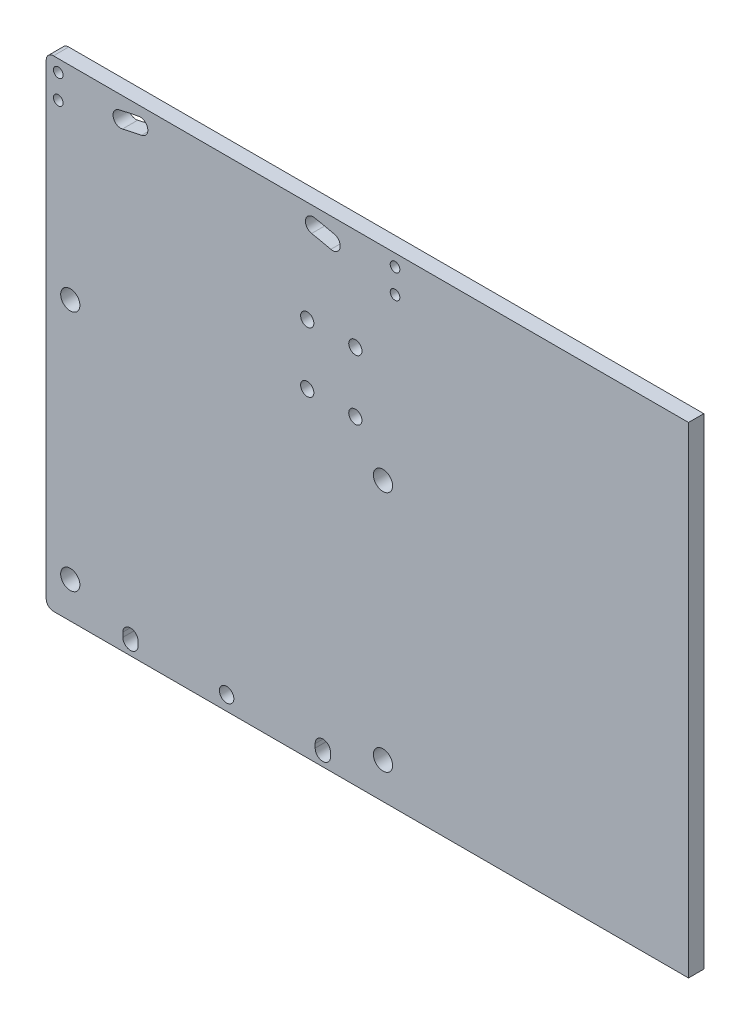
SolidWorks part; units mm, degrees
material "Plain Carbon Steel"
ref_plane "Front Plane" through (0, 0, 0) normal (0, 0, 1) x (1, 0, 0)
ref_plane "Top Plane" through (0, 0, 0) normal (0, 1, 0) x (1, 0, 0)
ref_plane "Right Plane" through (0, 0, 0) normal (1, 0, 0) x (0, 0, -1)
sketch "Sketch1" plane through (0, 0, 0) normal (0, 0, 1) x (1, 0, 0)
  line L0 (0, 0) -> (0, -65.325) construction
  line L1 (72, 134.675) -> (-72, 134.675)
  line L2 (75, 131.675) -> (75, -62.325)
  line L3 (72, -65.325) -> (-72, -65.325)
  line L4 (-75, 131.675) -> (-75, -62.325)
  line L5 (75, 134.675) -> (-75, -65.325) construction
  line L6 (75, -65.325) -> (-75, 134.675) construction
  line L7 (65, -50.325) -> (-65, -50.325) construction
  line L8 (65, -50.325) -> (65, 50.325) construction
  line L9 (65, 50.325) -> (-65, 50.325) construction
  line L10 (-65, -50.325) -> (-65, 50.325) construction
  line L11 (65, -50.325) -> (-65, 50.325) construction
  line L12 (65, 50.325) -> (-65, -50.325) construction
  line L13 (0, 34.675) -> (0, 0) construction
  circle A0 centre (-65, 50.325) radius 4
  circle A1 centre (-65, -50.325) radius 4
  circle A2 centre (65, -50.325) radius 4
  circle A3 centre (65, 50.325) radius 4
  arc A4 (-72, -65.325) -> (-75, -62.325) centre (-72, -62.325) cw
  arc A5 (75, -62.325) -> (72, -65.325) centre (72, -62.325) cw
  arc A6 (75, 131.675) -> (72, 134.675) centre (72, 131.675) ccw
  arc A7 (-72, 134.675) -> (-75, 131.675) centre (-72, 131.675) ccw
  circle A8 centre (-65, 50.325) radius 12.325 construction
  circle A9 centre (-65, -50.325) radius 12.325 construction
  point P0 (0, 0)
  point P6 (0, 0)
  point P32 (-65, -38)
  point P35 (-65, 38)
  dimension "D5" = 8
  dimension "D6" = 8
  dimension "D7" = 3
  dimension "D8" = 24.65
  dimension "D9" = 200
  dimension "D1" = 15
  dimension "D2" = 150
  dimension "D3" = 76
  dimension "D4" = 10
extrude "Boss-Extrude1" add sketch "Sketch1" along normal blind 6.35
sketch "Sketch2" plane through (0, 0, 6.35) normal (0, 0, 1) x (1, 0, 0)
  line L0 (-40, -59.325) -> (40, -59.325) construction
  line L1 (0, -59.325) -> (0, 126.675) construction
  line L2 (-40, 126.675) -> (40, 126.675) construction
  line L3 (-44.048, 125.7581) -> (0, -59.325) construction
  line L4 (0, -59.325) -> (-35.9329, 127.5033) construction
  line L5 (-39.9905, -58.4524) -> (0, -59.325) construction
  line L6 (-39.9905, -60.1976) -> (0, -59.325) construction
  line L7 (72, 134.675) -> (-72, 134.675) construction
  line L8 (-72, -65.325) -> (72, -65.325) construction
  line L9 (39.9905, -60.1976) -> (0, -59.325) construction
  line L10 (39.9905, -58.4524) -> (0, -59.325) construction
  line L11 (0, -59.325) -> (35.9329, 127.5033) construction
  line L12 (44.048, 125.7581) -> (0, -59.325) construction
  arc A4 (-35.9329, 127.5033) -> (-44.048, 125.7581) centre (0, -59.325) ccw construction
  arc A5 (-36.5335, 130.6261) -> (-44.7843, 128.8517) centre (0, -59.325) ccw
  arc A6 (-35.3323, 124.3806) -> (-43.3118, 122.6645) centre (0, -59.325) ccw
  arc A7 (-35.3323, 124.3806) -> (-36.5335, 130.6261) centre (-35.9329, 127.5033) ccw
  arc A8 (-44.7843, 128.8517) -> (-43.3118, 122.6645) centre (-44.048, 125.7581) ccw
  arc A9 (-39.9905, -58.4524) -> (-39.9905, -60.1976) centre (0, -59.325) ccw construction
  arc A10 (-43.1647, -58.3831) -> (-43.1647, -60.2669) centre (0, -59.325) ccw
  arc A11 (-36.8162, -58.5217) -> (-36.8162, -60.1283) centre (0, -59.325) ccw
  arc A12 (-36.8162, -58.5217) -> (-43.1647, -58.3831) centre (-39.9905, -58.4524) ccw
  arc A13 (-43.1647, -60.2669) -> (-36.8162, -60.1283) centre (-39.9905, -60.1976) ccw
  arc A14 (35.9329, 127.5033) -> (44.048, 125.7581) centre (0, -59.325) cw construction
  arc A15 (36.5335, 130.6261) -> (44.7843, 128.8517) centre (0, -59.325) cw
  arc A16 (35.3323, 124.3806) -> (43.3118, 122.6645) centre (0, -59.325) cw
  arc A17 (35.3323, 124.3806) -> (36.5335, 130.6261) centre (35.9329, 127.5033) cw
  arc A18 (44.7843, 128.8517) -> (43.3118, 122.6645) centre (44.048, 125.7581) cw
  arc A19 (39.9905, -58.4524) -> (39.9905, -60.1976) centre (0, -59.325) cw construction
  arc A20 (43.1647, -58.3831) -> (43.1647, -60.2669) centre (0, -59.325) cw
  arc A21 (36.8162, -58.5217) -> (36.8162, -60.1283) centre (0, -59.325) cw
  arc A22 (36.8162, -58.5217) -> (43.1647, -58.3831) centre (39.9905, -58.4524) cw
  arc A23 (43.1647, -60.2669) -> (36.8162, -60.1283) centre (39.9905, -60.1976) cw
  circle A24 centre (0, -59.325) radius 3
  point P2 (0, -59.325)
  point P10 (-40, -59.325)
  point P13 (0, 126.675)
  point P16 (-40, 126.675)
  point P36 (40, 126.675)
  point P41 (40, -59.325)
  dimension "D2" = 2.5
  dimension "D5" = 40
  dimension "D3" = 40
  dimension "D4" = 3.175
  dimension "D6" = 3.18
  dimension "D7" = 8
  dimension "D9" = 6
  dimension "D1" = 2.5
  dimension "D8" = 6
extrude "Cut-Extrude1" cut sketch "Sketch2" against normal blind 10
sketch "Sketch3" plane through (0, 0, 6.35) normal (0, 0, 1) x (1, 0, 0)
  line L0 (-70, 129.675) -> (-70, 119.675) construction
  line L1 (0, 134.675) -> (0, 111.0303) construction
  line L2 (72, 134.675) -> (-72, 134.675) construction
  line L3 (70, 129.675) -> (70, 119.675) construction
  line L4 (-75, 131.675) -> (-75, -62.325) construction
  circle A0 centre (-70, 129.675) radius 2
  circle A1 centre (-70, 119.675) radius 2
  circle A3 centre (70, 119.675) radius 2
  circle A4 centre (70, 129.675) radius 2
  dimension "D2" = 4
  dimension "D1" = 10
  dimension "D3" = 5
  dimension "D4" = 5
extrude "Cut-Extrude2" cut sketch "Sketch3" against normal through all
extrude "Cut-Extrude3" cut sketch "Sketch4" against normal blind 10
sketch "Sketch4" plane through (-33.8654, -165.328, 0) normal (0, 0, -1) x (-1, 0, 0)
  circle A4 centre (-67.3654, 232.8265) radius 2.75
  circle A5 centre (-87.3654, 232.8265) radius 2.75
  circle A6 centre (-87.3654, 257.8265) radius 2.75
  circle A7 centre (-67.3654, 257.8265) radius 2.75
sketch "Sketch5" plane through (0, 0, 6.35) normal (0, 0, 1) x (1, 0, 0)
  line L0 (72, 134.675) -> (192, 134.675)
  line L2 (192, 134.675) -> (192, -65.325)
  line L7 (72, -65.325) -> (192, -65.325)
  line L8 (75, -62.325) -> (75, 131.675) construction
  line L9 (75, -62.325) -> (75, 131.675)
  arc A0 (75, 131.675) -> (72, 134.675) centre (72, 131.675) ccw construction
  arc A1 (75, 131.675) -> (72, 134.675) centre (72, 131.675) ccw
  arc A2 (72, -65.325) -> (75, -62.325) centre (72, -62.325) ccw construction
  arc A3 (72, -65.325) -> (75, -62.325) centre (72, -62.325) ccw
  dimension "D1" = 120
extrude "Boss-Extrude2" add sketch "Sketch5" against normal up to surface (6.35 mm away) contours L0 L2 L7 A3 L9 A1 up to face at (30.75, 92.4985, 0)
